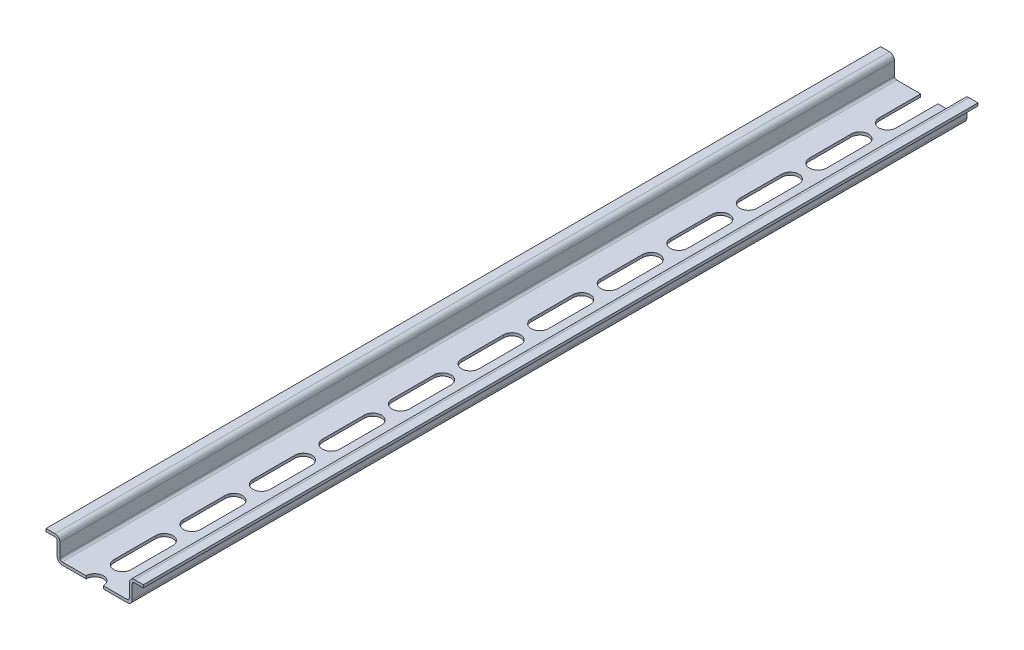
SolidWorks part; units mm, degrees
ref_plane "Front Plane" through (0, 0, 0) normal (0, 0, 1) x (1, 0, 0)
ref_plane "Top Plane" through (0, 0, 0) normal (0, 1, 0) x (1, 0, 0)
ref_plane "Right Plane" through (0, 0, 0) normal (1, 0, 0) x (0, 0, -1)
sketch "Sketch1" plane through (0, 0, 0) normal (0, 0, 1) x (1, 0, 0)
  line L0 (0, 0) -> (-11.7, 0)
  line L5 (-13.5, 1.8) -> (-13.5, 6.7)
  line L6 (-14.3, 7.5) -> (-17.5, 7.5)
  line L15 (0, 0) -> (0, 12.268) construction
  line L16 (0, 1) -> (-11.7, 1)
  line L17 (-12.5, 1.8) -> (-12.5, 6.7)
  line L18 (-14.3, 8.5) -> (-17.5, 8.5)
  line L19 (-17.5, 8.5) -> (-17.5, 7.5)
  line L20 (17.5, 8.5) -> (17.5, 7.5)
  line L21 (14.3, 8.5) -> (17.5, 8.5)
  line L22 (12.5, 1.8) -> (12.5, 6.7)
  line L23 (0, 1) -> (11.7, 1)
  line L24 (14.3, 7.5) -> (17.5, 7.5)
  line L25 (13.5, 1.8) -> (13.5, 6.7)
  line L26 (0, 0) -> (11.7, 0)
  arc A0 (-11.7, 0) -> (-13.5, 1.8) centre (-11.7, 1.8) cw
  arc A1 (-13.5, 6.7) -> (-14.3, 7.5) centre (-14.3, 6.7) ccw
  arc A2 (-11.7, 1) -> (-12.5, 1.8) centre (-11.7, 1.8) cw
  arc A3 (-12.5, 6.7) -> (-14.3, 8.5) centre (-14.3, 6.7) ccw
  arc A4 (12.5, 6.7) -> (14.3, 8.5) centre (14.3, 6.7) cw
  arc A5 (11.7, 1) -> (12.5, 1.8) centre (11.7, 1.8) ccw
  arc A6 (13.5, 6.7) -> (14.3, 7.5) centre (14.3, 6.7) cw
  arc A7 (11.7, 0) -> (13.5, 1.8) centre (11.7, 1.8) ccw
  point P0 (0, 0)
  point P6 (-13.5, 0)
  point P10 (-13.5, 7.5)
  point P16 (13.5, 7.5)
  point P31 (13.5, 0)
  dimension "D4" = 1.8
  dimension "D6" = 0.8
  dimension "D7" = 1.8
  dimension "D8" = 8.5
  dimension "D1" = 17.5
  dimension "D2" = 7.5
  dimension "D3" = 11.7
  dimension "D5" = 1
  dimension "D9" = 35
  dimension "D10" = 27
extrude "Boss-Extrude2" add sketch "Sketch1" along normal blind 300
sketch "Sketch2" plane through (0, 1, 0) normal (0, 1, 0) x (1, 0, 0)
  line L0 (0, -290) -> (0, -275) construction
  line L1 (-3.1, -290) -> (-3.1, -275)
  line L2 (3.1, -290) -> (3.1, -275)
  line L3 (0, -265) -> (0, -250) construction
  line L6 (-3.1, -265) -> (-3.1, -250)
  line L7 (3.1, -265) -> (3.1, -250)
  line L8 (11.7, 0) -> (-11.7, 0) construction
  line L9 (11.7, -300) -> (-11.7, -300) construction
  line L10 (0, -240) -> (0, -225) construction
  line L11 (-3.1, -240) -> (-3.1, -225)
  line L12 (3.1, -240) -> (3.1, -225)
  line L13 (0, -215) -> (0, -200) construction
  line L14 (-3.1, -215) -> (-3.1, -200)
  line L15 (3.1, -215) -> (3.1, -200)
  line L16 (0, -315) -> (0, -300) construction
  line L17 (-3.1, -315) -> (-3.1, -300)
  line L18 (3.1, -315) -> (3.1, -300)
  line L19 (0, -190) -> (0, -175) construction
  line L22 (-3.1, -190) -> (-3.1, -175)
  line L25 (3.1, -190) -> (3.1, -175)
  line L28 (0, -165) -> (0, -150) construction
  line L31 (-3.1, -165) -> (-3.1, -150)
  line L34 (3.1, -165) -> (3.1, -150)
  line L35 (0, -140) -> (0, -125) construction
  line L36 (-3.1, -140) -> (-3.1, -125)
  line L37 (3.1, -140) -> (3.1, -125)
  line L38 (0, -115) -> (0, -100) construction
  line L39 (-3.1, -115) -> (-3.1, -100)
  line L40 (3.1, -115) -> (3.1, -100)
  line L41 (0, -90) -> (0, -75) construction
  line L42 (-3.1, -90) -> (-3.1, -75)
  line L43 (3.1, -90) -> (3.1, -75)
  line L44 (0, -65) -> (0, -50) construction
  line L45 (-3.1, -65) -> (-3.1, -50)
  line L46 (3.1, -65) -> (3.1, -50)
  line L47 (0, -40) -> (0, -25) construction
  line L48 (-3.1, -40) -> (-3.1, -25)
  line L49 (3.1, -40) -> (3.1, -25)
  line L50 (0, -15) -> (0, 0) construction
  line L51 (-3.1, -15) -> (-3.1, 0)
  line L52 (3.1, -15) -> (3.1, 0)
  arc A0 (-3.1, -290) -> (3.1, -290) centre (0, -290) ccw
  arc A1 (3.1, -275) -> (-3.1, -275) centre (0, -275) ccw
  arc A4 (-3.1, -265) -> (3.1, -265) centre (0, -265) ccw
  arc A5 (3.1, -250) -> (-3.1, -250) centre (0, -250) ccw
  arc A6 (-3.1, -240) -> (3.1, -240) centre (0, -240) ccw
  arc A7 (3.1, -225) -> (-3.1, -225) centre (0, -225) ccw
  arc A8 (-3.1, -215) -> (3.1, -215) centre (0, -215) ccw
  arc A9 (3.1, -200) -> (-3.1, -200) centre (0, -200) ccw
  arc A10 (-3.1, -315) -> (3.1, -315) centre (0, -315) ccw
  arc A11 (3.1, -300) -> (-3.1, -300) centre (0, -300) ccw
  arc A22 (-3.1, -190) -> (3.1, -190) centre (0, -190) ccw
  arc A23 (3.1, -175) -> (-3.1, -175) centre (0, -175) ccw
  arc A24 (-3.1, -165) -> (3.1, -165) centre (0, -165) ccw
  arc A25 (3.1, -150) -> (-3.1, -150) centre (0, -150) ccw
  arc A26 (-3.1, -140) -> (3.1, -140) centre (0, -140) ccw
  arc A27 (3.1, -125) -> (-3.1, -125) centre (0, -125) ccw
  arc A28 (-3.1, -115) -> (3.1, -115) centre (0, -115) ccw
  arc A29 (3.1, -100) -> (-3.1, -100) centre (0, -100) ccw
  arc A30 (-3.1, -90) -> (3.1, -90) centre (0, -90) ccw
  arc A31 (3.1, -75) -> (-3.1, -75) centre (0, -75) ccw
  arc A32 (-3.1, -65) -> (3.1, -65) centre (0, -65) ccw
  arc A33 (3.1, -50) -> (-3.1, -50) centre (0, -50) ccw
  arc A34 (-3.1, -40) -> (3.1, -40) centre (0, -40) ccw
  arc A35 (3.1, -25) -> (-3.1, -25) centre (0, -25) ccw
  arc A36 (-3.1, -15) -> (3.1, -15) centre (0, -15) ccw
  arc A37 (3.1, 0) -> (-3.1, 0) centre (0, 0) ccw
  point P3 (0, -282.5)
  point P10 (0, -257.5)
  point P18 (0, 0)
  point P22 (0, -300)
  point P24 (0, -182.5)
  point P27 (0, -232.5)
  point P35 (0, -207.5)
  point P43 (0, -307.5)
  point P52 (0, -157.5)
  point P59 (0, -132.5)
  point P66 (0, -107.5)
  point P73 (0, -82.5)
  point P80 (0, -57.5)
  point P87 (0, -32.5)
  point P94 (0, -7.5)
  dimension "D1" = 15
  dimension "D2" = 6.2
  dimension "D5" = 25
  dimension "D6" = 10
  dimension "D8" = 25
  dimension "D11" = 25
  dimension "D14" = 25
  dimension "D3" = 15
  dimension "D4" = 6.2
  dimension "D7" = 15
  dimension "D9" = 6.2
  dimension "D10" = 15
  dimension "D12" = 6.2
  dimension "D13" = 15
  dimension "D15" = 6.2
  dimension "D16" = 2
  dimension "D17" = 25
  dimension "D18" = 4
  dimension "D19" = 5
extrude "Cut-Extrude1" cut sketch "Sketch2" against normal blind 100
